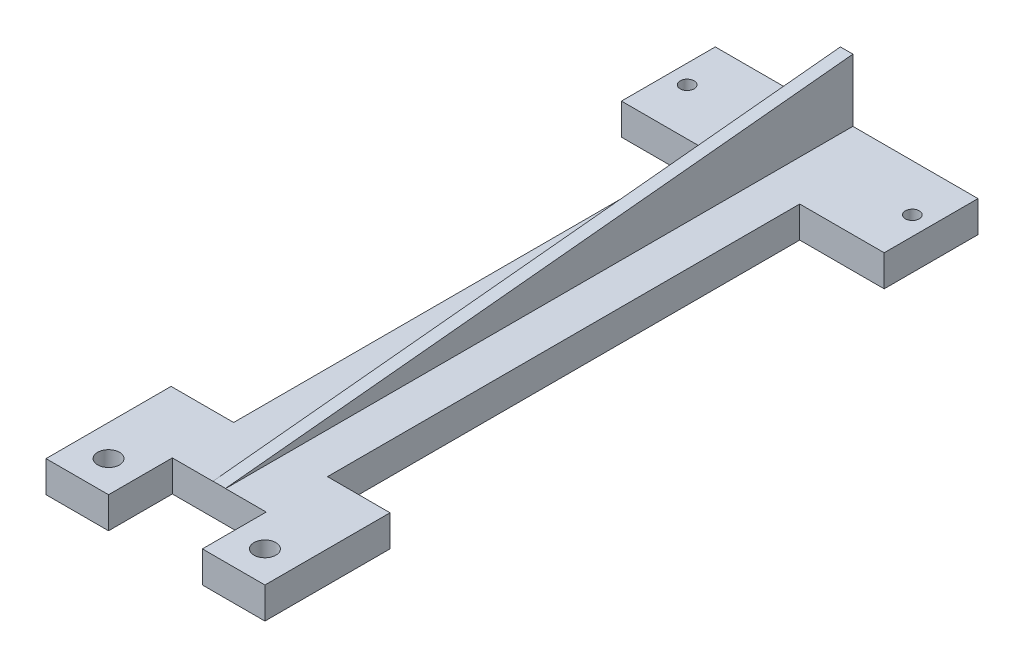
SolidWorks part; units mm, degrees
ref_plane "Front Plane" through (0, 0, 0) normal (0, 0, 1) x (1, 0, 0)
ref_plane "Top Plane" through (0, 0, 0) normal (0, 1, 0) x (1, 0, 0)
ref_plane "Right Plane" through (0, 0, 0) normal (1, 0, 0) x (0, 0, -1)
sketch "Sketch1" plane through (0, 0, 0) normal (0, 1, 0) x (1, 0, 0)
  line L1 (0, 0) -> (42, 0)
  line L2 (0, 0) -> (0, 15)
  line L3 (0, 15) -> (42, 15)
  line L4 (42, 0) -> (42, 15)
  dimension "D1" = 42
  dimension "D2" = 15
extrude "Boss-Extrude1" add sketch "Sketch1" along normal blind 5
sketch "Sketch2" plane through (0, 5, 0) normal (0, 1, 0) x (1, 0, 0)
  line L0 (3, 7.5) -> (39, 7.5) construction
  line L3 (21, 15) -> (21, 0) construction
  line L4 (42, 15) -> (0, 15) construction
  line L5 (0, 0) -> (42, 0) construction
  circle A0 centre (3, 7.5) radius 1.115
  circle A1 centre (39, 7.5) radius 1.115
  point P2 (21, 7.5)
  point P3 (21, 7.5)
  dimension "D2" = 2.23
  dimension "D1" = 36
extrude "Cut-Extrude1" cut sketch "Sketch2" against normal through all
sketch "Sketch3" plane through (0, 5, 0) normal (0, 1, 0) x (1, 0, 0)
  line L0 (0, 0) -> (42, 0) construction
  line L1 (13.5, 0) -> (28.5, 0)
  line L2 (13.5, 0) -> (13.5, -75.5)
  line L3 (13.5, -75.5) -> (28.5, -75.5)
  line L4 (28.5, 0) -> (28.5, -75.5)
  point P4 (21, 0)
  point P7 (21, 0)
  dimension "D1" = 15
  dimension "D2" = 75.5
extrude "Boss-Extrude2" add sketch "Sketch3" against normal up to surface (5 mm away) up to face at (3, 0, -6.385)
sketch "Sketch4" plane through (0, 5, 0) normal (0, 1, 0) x (1, 0, 0)
  line L0 (13.5, -75.5) -> (28.5, -75.5) construction
  line L1 (3.5, -75.5) -> (38.5, -75.5)
  line L2 (3.5, -75.5) -> (3.5, -85.5)
  line L3 (3.5, -85.5) -> (38.5, -85.5)
  line L4 (38.5, -75.5) -> (38.5, -85.5)
  point P4 (21, -75.5)
  point P7 (21, -75.5)
  dimension "D1" = 10
  dimension "D2" = 35
extrude "Boss-Extrude3" add sketch "Sketch4" against normal up to surface (5 mm away) up to face at (3, 0, -6.385)
sketch "Sketch5" plane through (0, 5, 0) normal (0, 1, 0) x (1, 0, 0)
  line L0 (3.5, -85.5) -> (13.5, -95.5) construction
  line L1 (3.5, -85.5) -> (13.5, -85.5)
  line L2 (3.5, -85.5) -> (3.5, -95.5)
  line L3 (3.5, -95.5) -> (13.5, -95.5)
  line L4 (13.5, -85.5) -> (13.5, -95.5)
  line L5 (38.5, -85.5) -> (28.5, -85.5)
  line L6 (38.5, -85.5) -> (38.5, -95.5)
  line L7 (38.5, -95.5) -> (28.5, -95.5)
  line L8 (28.5, -85.5) -> (28.5, -95.5)
  line L9 (28.5, -85.5) -> (38.5, -95.5) construction
  dimension "D1" = 10
  dimension "D2" = 10
extrude "Boss-Extrude4" add sketch "Sketch5" against normal up to surface (5 mm away) up to face at (3, 0, -6.385)
sketch "Sketch6" plane through (0, 5, 0) normal (0, 1, 0) x (1, 0, 0)
  line L0 (13.5, -95.5) -> (3.5, -85.5) construction
  line L1 (3.5, -75.5) -> (3.5, -95.5) construction
  line L2 (38.5, -95.5) -> (28.5, -85.5) construction
  line L3 (13.5, -85.5) -> (28.5, -85.5) construction
  circle A0 centre (8.5, -90.5) radius 1.75
  circle A1 centre (33.5, -90.5) radius 1.75
  dimension "D1" = 3.5
extrude "Cut-Extrude2" cut sketch "Sketch6" against normal through all
sketch "Sketch7" plane through (0, 5, 0) normal (0, 1, 0) x (1, 0, 0)
  line L2 (13.5, -85.3) -> (28.5, -85.3)
  line L3 (13.5, -85.3) -> (28.5, -85.3)
  line L6 (13.5, -85.3) -> (13.5, -85.5)
  line L7 (13.5, -85.5) -> (28.5, -85.5)
  line L8 (28.5, -85.5) -> (28.5, -85.3)
  dimension "D1" = 0.2
extrude "Cut-Extrude3" cut sketch "Sketch7" against normal through all
sketch "Sketch8" plane through (0, 5, 0) normal (0, 1, 0) x (1, 0, 0)
  line L0 (42, 15) -> (0, 15) construction
  line L1 (20, 15) -> (22, 15)
  line L2 (20, 15) -> (20, -85.3)
  line L3 (20, -85.3) -> (22, -85.3)
  line L4 (22, 15) -> (22, -85.3)
  line L5 (28.5, -85.3) -> (13.5, -85.3) construction
  point P8 (21, -85.3)
  point P9 (21, -85.3)
  dimension "D1" = 2
extrude "Boss-Extrude5" add sketch "Sketch8" along normal blind 10
sketch "Sketch9" plane through (20, 0, 0) normal (-1, 0, 0) x (0, 0, 1)
  line L0 (-15, 15) -> (85.5, 5)
  line L1 (75.5, 5) -> (95.5, 5) construction
  line L2 (85.5, 5) -> (85.3, 15)
  line L3 (85.3, 15) -> (-15, 15)
extrude "Cut-Extrude4" cut sketch "Sketch9" against normal through all
